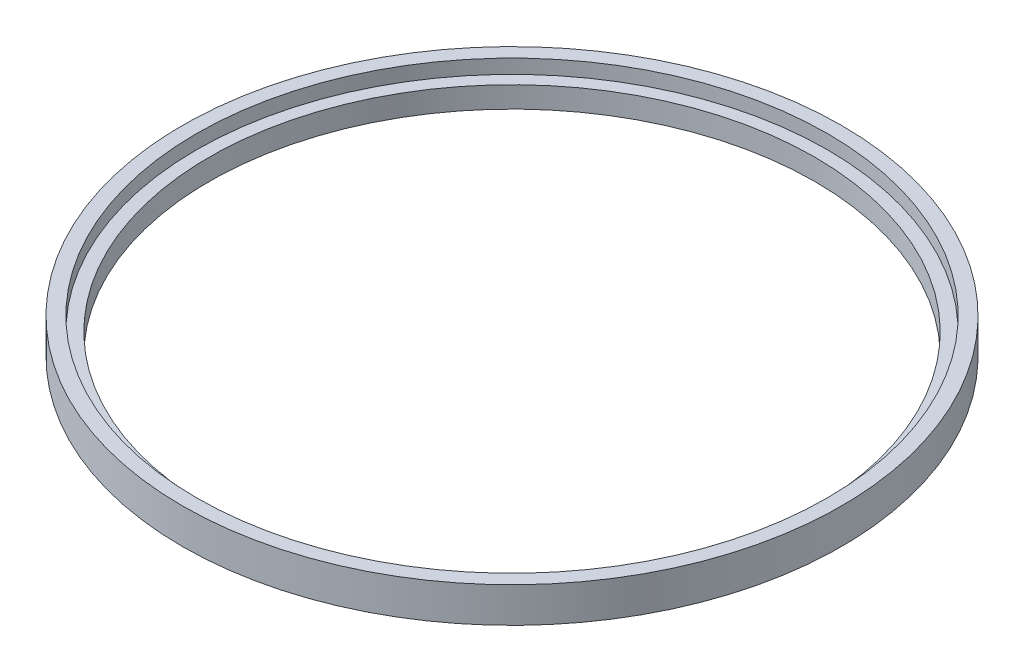
SolidWorks part; units mm, degrees
ref_plane "Front Plane" through (0, 0, 0) normal (0, 0, 1) x (1, 0, 0)
ref_plane "Top Plane" through (0, 0, 0) normal (0, 1, 0) x (1, 0, 0)
ref_plane "Right Plane" through (0, 0, 0) normal (1, 0, 0) x (0, 0, -1)
sketch "Sketch1" plane through (0, 0, 0) normal (0, 1, 0) x (1, 0, 0)
  circle A0 centre (0, 0) radius 21.5
  circle A1 centre (0, 0) radius 23.4
  dimension "D1" = 43
  dimension "D2" = 1.9
extrude "Boss-Extrude1" add sketch "Sketch1" along normal blind 1.5
sketch "Sketch2" plane through (0, 1.5, 0) normal (0, 1, 0) x (1, 0, 0)
  circle A0 centre (0, 0) radius 23.4 construction
  circle A1 centre (0, 0) radius 23.4
  circle A2 centre (0, 0) radius 22.4
  dimension "D1" = 1
extrude "Boss-Extrude2" add sketch "Sketch2" along normal blind 1
